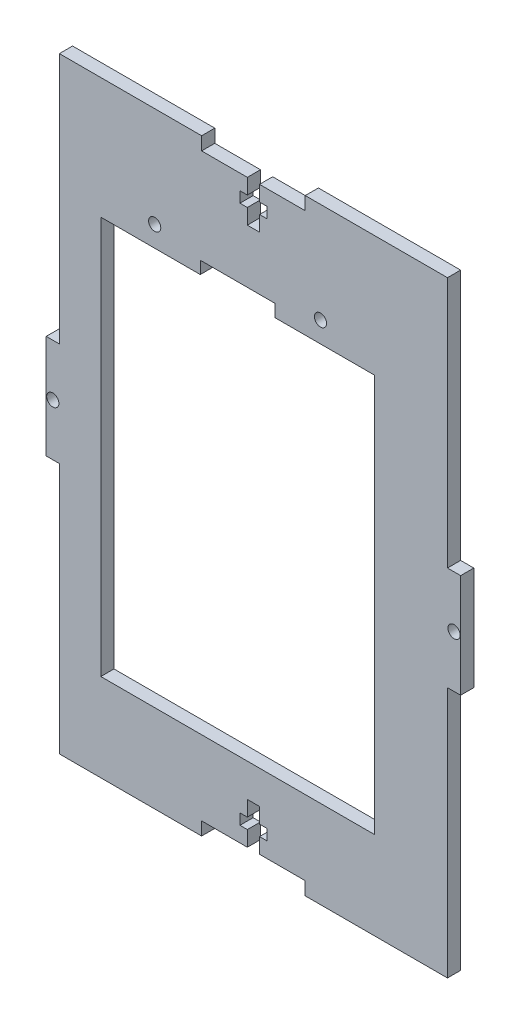
SolidWorks part; units mm, degrees
ref_plane "Front Plane" through (0, 0, 0) normal (0, 0, 1) x (1, 0, 0)
ref_plane "Top Plane" through (0, 0, 0) normal (0, 1, 0) x (1, 0, 0)
ref_plane "Right Plane" through (0, 0, 0) normal (1, 0, 0) x (0, 0, -1)
sketch "Sketch1" plane through (0, 0, 0) normal (0, 0, 1) x (1, 0, 0)
  line L0 (0, 73.175) -> (0, -73.175) construction
  line L1 (-46.825, 73.175) -> (46.825, 73.175)
  line L2 (-46.825, 73.175) -> (-46.825, -73.175)
  line L3 (-46.825, -73.175) -> (46.825, -73.175)
  line L4 (46.825, 73.175) -> (46.825, -73.175)
  line L5 (-46.825, 73.175) -> (46.825, -73.175) construction
  line L6 (-46.825, -73.175) -> (46.825, 73.175) construction
  line L7 (-46.825, 0) -> (46.825, 0) construction
  line L8 (-3.25, -63.7) -> (3.25, -63.7)
  line L9 (12.5, 73.175) -> (-12.5, 73.175)
  line L10 (12.5, 73.175) -> (12.5, 70)
  line L11 (12.5, 70) -> (-12.5, 70)
  line L12 (-12.5, 73.175) -> (-12.5, 70)
  line L13 (12.5, 73.175) -> (-12.5, 70) construction
  line L14 (12.5, 70) -> (-12.5, 73.175) construction
  line L15 (-1.47, 70) -> (1.47, 70)
  line L16 (-1.47, 70) -> (-1.47, 60)
  line L17 (-1.47, 60) -> (1.47, 60)
  line L18 (1.47, 70) -> (1.47, 60)
  line L19 (-1.47, 70) -> (1.47, 60) construction
  line L20 (-1.47, 60) -> (1.47, 70) construction
  line L21 (-3.25, 66.3) -> (3.25, 66.3)
  line L22 (-3.25, 66.3) -> (-3.25, 63.7)
  line L23 (-3.25, 63.7) -> (3.25, 63.7)
  line L24 (3.25, 66.3) -> (3.25, 63.7)
  line L25 (-3.25, 66.3) -> (3.25, 63.7) construction
  line L26 (-3.25, 63.7) -> (3.25, 66.3) construction
  line L27 (3.25, -66.3) -> (3.25, -63.7)
  line L28 (-3.25, -66.3) -> (3.25, -66.3)
  line L29 (-3.25, -66.3) -> (-3.25, -63.7)
  line L30 (-1.47, -60) -> (1.47, -60)
  line L31 (1.47, -70) -> (1.47, -60)
  line L32 (-1.47, -70) -> (1.47, -70)
  line L33 (-1.47, -70) -> (-1.47, -60)
  line L34 (12.5, -70) -> (-12.5, -70)
  line L35 (-12.5, -73.175) -> (-12.5, -70)
  line L36 (12.5, -73.175) -> (-12.5, -73.175)
  line L37 (12.5, -73.175) -> (12.5, -70)
  line L38 (50, -12.5) -> (46.825, -12.5)
  line L39 (-50, 12.5) -> (-46.825, 12.5)
  line L40 (-50, 12.5) -> (-50, -12.5)
  line L41 (-50, -12.5) -> (-46.825, -12.5)
  line L42 (-46.825, 12.5) -> (-46.825, -12.5)
  line L43 (-50, 12.5) -> (-46.825, -12.5) construction
  line L44 (-50, -12.5) -> (-46.825, 12.5) construction
  line L45 (46.825, 12.5) -> (46.825, -12.5)
  line L46 (50, 12.5) -> (46.825, 12.5)
  line L47 (50, 12.5) -> (50, -12.5)
  circle A0 centre (-48.4125, 0) radius 1.47
  circle A1 centre (48.4125, 0) radius 1.47
  point P0 (0, 0)
  point P10 (0, 71.5875)
  point P15 (0, 65)
  point P20 (0, 65)
  point P37 (-48.4125, 0)
  dimension "D11" = 2.94
  dimension "D1" = 146.35
  dimension "D2" = 93.65
  dimension "D3" = 3.175
  dimension "D4" = 10
  dimension "D5" = 2.94
  dimension "D6" = 25
  dimension "D7" = 6.5
  dimension "D8" = 2.6
  dimension "D9" = 6.3
  dimension "D10" = 3.175
extrude "Boss-Extrude1" add sketch "Sketch1" along normal mid plane 3.175 contours L21 L24 L23 L18 L17 L16 L22 L11 L12 L1 L2 L3 L4 L10 | L40 L39 L42 L41 | A0 | L38 L45 L46 L47 | A1
sketch "Sketch2" plane through (0, 0, 1.5875) normal (0, 0, 1) x (1, 0, 0)
  circle A0 centre (16.175, 49) radius 1.47
  circle A1 centre (-23.825, 49) radius 1.47
extrude "Cut-Extrude1" cut sketch "Sketch2" against normal through all
sketch "Sketch3" plane through (0, 0, 1.5875) normal (0, 0, 1) x (1, 0, 0)
  line L0 (-36.825, 44) -> (29.175, 44) construction
  line L1 (29.175, 44) -> (29.175, -52) construction
  line L2 (29.175, -52) -> (-36.825, -52) construction
  line L3 (-36.825, -52) -> (-36.825, 44) construction
  line L5 (-12.825, 44) -> (-12.825, 47) construction
  line L6 (-12.825, 47) -> (5.175, 47) construction
  line L7 (5.175, 47) -> (5.175, 44) construction
  line L8 (-36.825, 44) -> (-12.825, 44)
  line L9 (29.175, 44) -> (29.175, -52)
  line L10 (29.175, -52) -> (-36.825, -52)
  line L11 (-36.825, -52) -> (-36.825, 44)
  line L13 (-12.825, 44) -> (-12.825, 47)
  line L14 (-12.825, 47) -> (5.175, 47)
  line L15 (5.175, 47) -> (5.175, 44)
  line L16 (5.175, 44) -> (29.175, 44)
extrude "Cut-Extrude3" cut sketch "Sketch3" against normal through all and the other way through all
